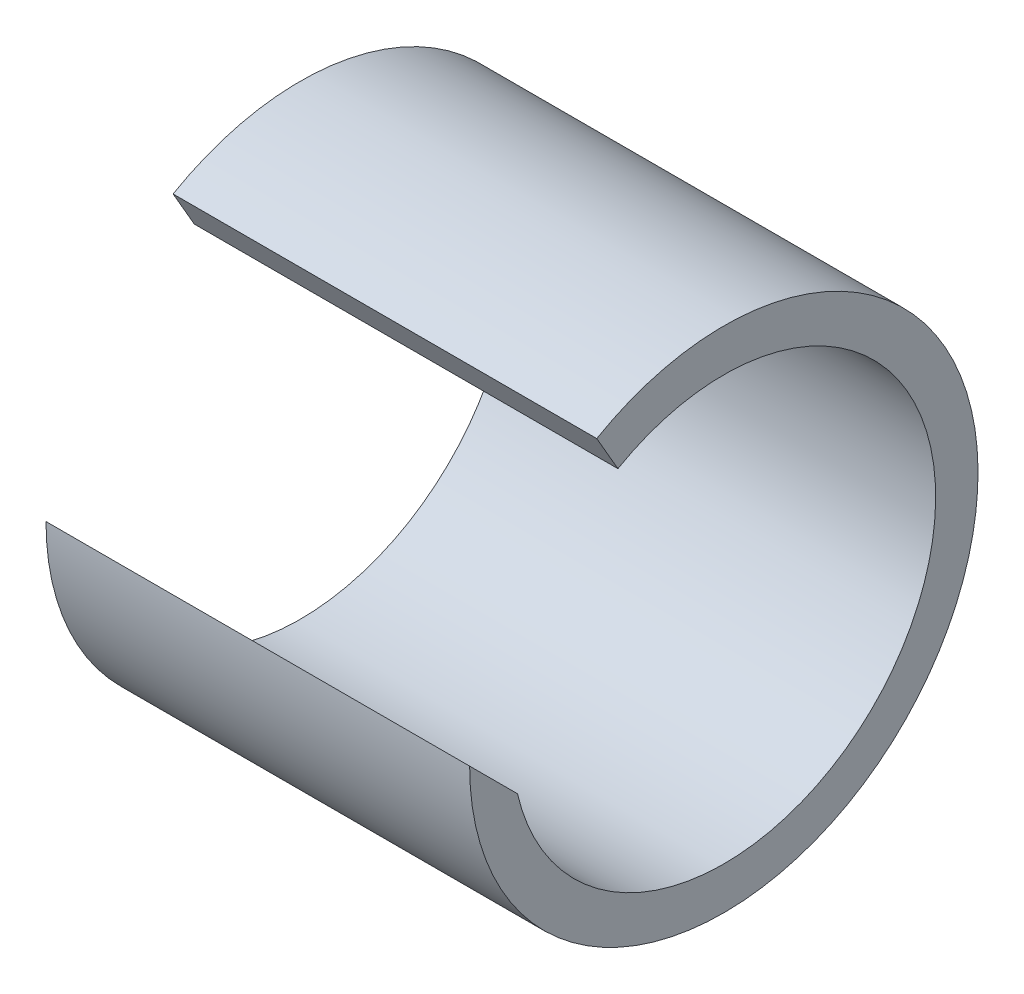
SolidWorks part; units mm, degrees
ref_plane "Front Plane" through (0, 0, 0) normal (0, 0, 1) x (1, 0, 0)
ref_plane "Top Plane" through (0, 0, 0) normal (0, 1, 0) x (1, 0, 0)
ref_plane "Right Plane" through (0, 0, 0) normal (1, 0, 0) x (0, 0, -1)
sketch "Sketch1" plane through (0, 0, 0) normal (1, 0, 0) x (0, 0, -1)
  circle A0 centre (0, 0) radius 19.05
  circle A1 centre (0, 0) radius 15.875
  dimension "D1" = 38.1
  dimension "D2" = 3.175
extrude "Boss-Extrude1" add sketch "Sketch1" along normal blind 31.75
sketch "Sketch2" plane through (31.75, 0, 0) normal (1, 0, 0) x (0, 0, -1)
  line L0 (-15.875, 0) -> (-19.05, 0)
  line L1 (-7.9375, 13.7482) -> (-9.525, 16.4978)
  circle A0 centre (0, 0) radius 19.05 construction
  arc A1 (-19.05, 0) -> (-9.525, 16.4978) centre (0, 0) cw
  arc A2 (-15.875, 0) -> (-7.9375, 13.7482) centre (0, 0) cw
  circle A3 centre (0, 0) radius 15.875 construction
  dimension "D1" = 60
  dimension "D2" = 3.175
extrude "Cut-Extrude2" cut sketch "Sketch2" against normal through all
sketch "Sketch3" plane through (31.75, 0, 0) normal (1, 0, 0) x (0, 0, -1)
  line L0 (-19.05, 0) -> (-15.875, 0)
  line L1 (-19.05, 0) -> (-15.4649, -3.5851)
  arc A0 (-15.875, 0) -> (-7.9375, 13.7482) centre (0, 0) ccw construction
  arc A1 (-15.4649, -3.5851) -> (-15.875, 0) centre (0, 0) cw
  dimension "D1" = 45
extrude "Cut-Extrude3" cut sketch "Sketch3" against normal through all
